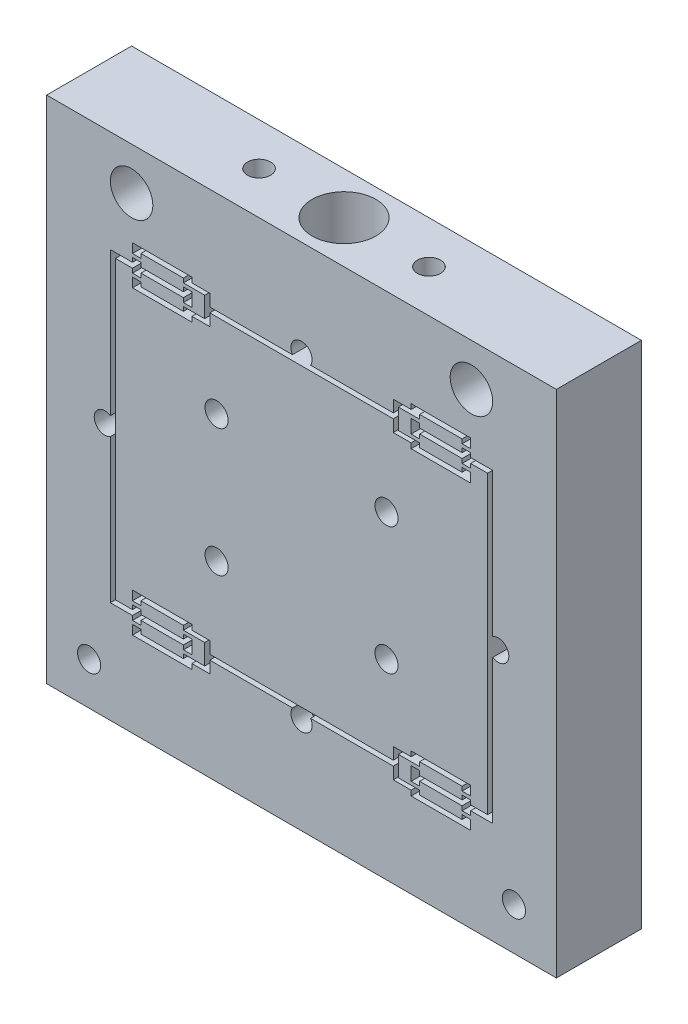
SolidWorks part; units mm, degrees
ref_plane "Front Plane" through (0, 0, 0) normal (0, 0, 1) x (1, 0, 0)
ref_plane "Top Plane" through (0, 0, 0) normal (0, 1, 0) x (1, 0, 0)
ref_plane "Right Plane" through (0, 0, 0) normal (1, 0, 0) x (0, 0, -1)
sketch "Sketch1" plane through (0, 0, 0) normal (0, 0, 1) x (1, 0, 0)
  line L1 (-38.1, 38.1) -> (38.1, 38.1)
  line L2 (-38.1, 38.1) -> (-38.1, -38.1)
  line L3 (-38.1, -38.1) -> (38.1, -38.1)
  line L4 (38.1, 38.1) -> (38.1, -38.1)
  dimension "D1" = 38.1
  dimension "D2" = 38.1
  dimension "D3" = 38.1
  dimension "D4" = 38.1
extrude "Boss-Extrude1" add sketch "Sketch1" along normal mid plane 12.7
sketch "Sketch2" plane through (0, 0, 6.35) normal (0, 0, 1) x (1, 0, 0)
  line L0 (16.383, 23.495) -> (17.653, 23.495)
  line L1 (28.575, 22.86) -> (28.575, -22.86)
  line L2 (0, 0) -> (38.1, 0) construction
  line L3 (25.273, -22.86) -> (28.575, -22.86)
  line L4 (25.273, -22.098) -> (27.813, -22.098)
  line L5 (27.813, -22.098) -> (27.813, 22.098)
  line L6 (17.653, 23.495) -> (17.653, 22.86)
  line L7 (16.383, 21.463) -> (16.383, 23.495)
  line L8 (38.1, -38.1) -> (38.1, 38.1) construction
  line L9 (17.653, 22.86) -> (24.003, 22.86)
  line L10 (24.003, 22.86) -> (24.003, 23.495)
  line L11 (24.003, 23.495) -> (25.273, 23.495)
  line L12 (25.273, 23.495) -> (25.273, 22.86)
  line L13 (25.273, 22.86) -> (28.575, 22.86)
  line L14 (16.383, 21.463) -> (17.653, 21.463)
  line L15 (17.653, 21.463) -> (17.653, 22.098)
  line L16 (17.653, 22.098) -> (24.003, 22.098)
  line L17 (24.003, 22.098) -> (24.003, 21.463)
  line L18 (24.003, 21.463) -> (25.273, 21.463)
  line L19 (25.273, 21.463) -> (25.273, 22.098)
  line L20 (25.273, 22.098) -> (27.813, 22.098)
  line L21 (17.653, -23.495) -> (17.653, -22.86)
  line L22 (17.653, -22.86) -> (24.003, -22.86)
  line L23 (24.003, -22.86) -> (24.003, -23.495)
  line L24 (24.003, -23.495) -> (25.273, -23.495)
  line L25 (25.273, -23.495) -> (25.273, -22.86)
  line L26 (25.273, -21.463) -> (25.273, -22.098)
  line L27 (24.003, -21.463) -> (25.273, -21.463)
  line L28 (24.003, -22.098) -> (24.003, -21.463)
  line L29 (17.653, -22.098) -> (24.003, -22.098)
  line L30 (17.653, -21.463) -> (17.653, -22.098)
  line L31 (16.383, -21.463) -> (17.653, -21.463)
  line L32 (16.383, -21.463) -> (16.383, -23.495)
  line L33 (16.383, -23.495) -> (17.653, -23.495)
  dimension "D1" = 0.762
  dimension "D2" = 1.27
  dimension "D3" = 9.525
  dimension "D4" = 1.27
  dimension "D5" = 2.54
  dimension "D6" = 0.762
  dimension "D7" = 22.86
  dimension "D8" = 0.635
  dimension "D9" = 0.635
  dimension "D10" = 6.35
extrude "Cut-Extrude1" cut sketch "Sketch2" against normal up to next (12.7 mm away)
mirror "Mirror1" about plane through (0, 0, 0) normal (1, 0, 0) of "Cut-Extrude1"
sketch "Sketch3" plane through (0, 0, 6.35) normal (0, 0, 1) x (1, 0, 0)
  line L0 (25.273, 20.955) -> (25.273, 19.558)
  line L1 (25.273, 25.4) -> (16.383, 25.4)
  line L2 (16.383, 25.4) -> (16.383, 24.638)
  line L3 (-13.716, 22.86) -> (13.716, 22.86)
  line L6 (14.478, 24.003) -> (17.653, 24.003)
  line L7 (17.653, 24.003) -> (17.653, 24.638)
  line L8 (0, 38.1) -> (0, 0) construction
  line L9 (38.1, 38.1) -> (-38.1, 38.1) construction
  line L10 (25.273, 22.86) -> (25.273, 23.495) construction
  line L11 (24.003, 22.098) -> (24.003, 21.463) construction
  line L12 (17.653, 21.463) -> (17.653, 22.098) construction
  line L13 (13.716, 22.098) -> (-13.716, 22.098)
  line L14 (16.383, 24.638) -> (13.716, 24.638)
  line L15 (13.716, 24.638) -> (13.716, 22.86)
  line L16 (25.273, 25.4) -> (25.273, 24.003)
  line L17 (17.653, 24.638) -> (24.003, 24.638)
  line L18 (14.478, 24.003) -> (14.478, 20.955)
  line L19 (14.478, 20.955) -> (17.653, 20.955)
  line L20 (24.003, 21.463) -> (25.273, 21.463) construction
  line L21 (25.273, 23.495) -> (24.003, 23.495) construction
  line L25 (16.383, 23.495) -> (16.383, 21.463) construction
  line L26 (24.003, 24.638) -> (24.003, 24.003)
  line L27 (24.003, 24.003) -> (25.273, 24.003)
  line L28 (17.653, 20.955) -> (17.653, 20.32)
  line L29 (17.653, 20.32) -> (24.003, 20.32)
  line L30 (24.003, 20.32) -> (24.003, 20.955)
  line L31 (24.003, 20.955) -> (25.273, 20.955)
  line L32 (-16.383, 19.558) -> (-25.273, 19.558)
  line L33 (-16.383, 20.32) -> (-16.383, 19.558)
  line L34 (-25.273, 20.955) -> (-25.273, 19.558)
  line L35 (-24.003, 20.955) -> (-25.273, 20.955)
  line L36 (-24.003, 20.32) -> (-24.003, 20.955)
  line L37 (-17.653, 20.32) -> (-24.003, 20.32)
  line L38 (-17.653, 20.955) -> (-17.653, 20.32)
  line L39 (-14.478, 20.955) -> (-17.653, 20.955)
  line L40 (-14.478, 24.003) -> (-14.478, 20.955)
  line L41 (-14.478, 24.003) -> (-17.653, 24.003)
  line L42 (-17.653, 24.003) -> (-17.653, 24.638)
  line L43 (-17.653, 24.638) -> (-24.003, 24.638)
  line L44 (-24.003, 24.638) -> (-24.003, 24.003)
  line L45 (-24.003, 24.003) -> (-25.273, 24.003)
  line L46 (-25.273, 25.4) -> (-25.273, 24.003)
  line L47 (-13.716, 20.32) -> (-16.383, 20.32)
  line L48 (-13.716, 22.098) -> (-13.716, 20.32)
  line L49 (17.653, 22.098) -> (24.003, 22.098) construction
  line L50 (24.003, 22.86) -> (17.653, 22.86) construction
  line L51 (13.716, 22.098) -> (13.716, 20.32)
  line L52 (13.716, 20.32) -> (16.383, 20.32)
  line L53 (16.383, 20.32) -> (16.383, 19.558)
  line L54 (16.383, 19.558) -> (25.273, 19.558)
  line L55 (-13.716, 24.638) -> (-13.716, 22.86)
  line L56 (-16.383, 24.638) -> (-13.716, 24.638)
  line L57 (-16.383, 25.4) -> (-16.383, 24.638)
  line L58 (-25.273, 25.4) -> (-16.383, 25.4)
  point P26 (0, 17.78)
  point P35 (0, 19.05)
  dimension "D1" = 0.762
  dimension "D2" = 0.762
  dimension "D3" = 0.508
  dimension "D4" = 0.508
  dimension "D5" = 0.635
  dimension "D6" = 0.635
  dimension "D7" = 1.905
  dimension "D8" = 0.762
extrude "Cut-Extrude2" cut sketch "Sketch3" against normal up to next (12.7 mm away)
mirror "Mirror2" about plane through (0, 0, 0) normal (0, 1, 0) of "Cut-Extrude2"
hole_wizard "1/4 (0.25) Diameter Hole1" positions "Sketch5" profile "Sketch4" hole size "1/4" standard "ANSI Inch" end condition up to next
sketch "Sketch5" plane through (0, 0, 6.35) normal (0, 0, 1) x (1, 0, 0)
  line L0 (38.1, 38.1) -> (-38.1, 38.1) construction
  point P0 (-25.4, 31.75)
  point P2 (25.4, 31.75)
  dimension "D1" = 25.4
  dimension "D2" = 25.4
  dimension "D3" = 6.35
sketch "Sketch4" plane through (-25.4, 31.75, 6.35) normal (1, 0, 0) x (0, -1, 0)
  line L0 (0, 0) -> (0, 12.7)
  line L1 (0, 12.7) -> (3.175, 12.7)
  line L2 (3.175, 12.7) -> (3.175, 0)
  line L5 (3.175, 0) -> (0, 0)
  line L11 (0, -6.35) -> (0, 107.95) construction
  dimension "Thru Hole Dia." = 6.35
  dimension "Thru Hole Depth" = 12.7
hole_wizard "#8-32 Tapped Hole1" positions "Sketch7" profile "Sketch6" tap size "#8-32" standard "ANSI Inch" end condition up to next
sketch "Sketch7" plane through (0, 0, 6.35) normal (0, 0, 1) x (1, 0, 0)
  line L0 (-38.1, 38.1) -> (-38.1, -38.1) construction
  line L1 (38.1, -38.1) -> (38.1, 38.1) construction
  line L2 (-38.1, -38.1) -> (38.1, -38.1) construction
  point P0 (-12.7, 9.525)
  point P2 (12.7, 9.525)
  point P4 (12.7, -9.525)
  point P6 (-12.7, -9.525)
  point P20 (-31.75, -31.75)
  point P22 (31.75, -31.75)
  dimension "D1" = 12.7
  dimension "D2" = 12.7
  dimension "D3" = 9.525
  dimension "D4" = 9.525
  dimension "D5" = 6.35
  dimension "D6" = 6.35
  dimension "D7" = 6.35
sketch "Sketch6" plane through (-12.7, 9.525, 6.35) normal (1, 0, 0) x (0, -1, 0)
  line L0 (0, 0) -> (0, 12.7)
  line L1 (0, 12.7) -> (1.7272, 12.7)
  line L2 (1.7272, 12.7) -> (1.7272, 0)
  line L5 (1.7272, 0) -> (0, 0)
  line L11 (0, -6.35) -> (0, 107.95) construction
  dimension "Thru Tap Drill Dia." = 3.4544
  dimension "Thru Tap Drill Depth" = 12.7
cosmetic thread "Hole Thread1" parameters "D2"=4.1656
cosmetic thread "Hole Thread2" parameters "D2"=4.1656
cosmetic thread "Hole Thread3" parameters "D2"=4.1656
cosmetic thread "Hole Thread4" parameters "D2"=4.1656
cosmetic thread "Hole Thread5" parameters "D2"=4.1656
cosmetic thread "Hole Thread6" parameters "D2"=4.1656
sketch "Sketch12" plane through (0, 38.1, 0) normal (0, 1, 0) x (1, 0, 0)
  circle A0 centre (0, 0) radius 3.81
extrude "Cut-Extrude7" cut sketch "Sketch12" against normal blind 20.828
hole_wizard "#8-32 Tapped Hole2" positions "Sketch15" profile "Sketch14" tap size "#8-32" standard "ANSI Inch"
sketch "Sketch15" plane through (0, 38.1, 0) normal (0, 1, 0) x (1, 0, 0)
  point P0 (-12.7, 0)
  point P2 (12.7, 0)
  dimension "D1" = 12.7
  dimension "D2" = 12.7
sketch "Sketch14" plane through (-12.7, 38.1, 0) normal (1, 0, 0) x (0, 0, 1)
  line L0 (0, 0) -> (0, 11.1978)
  line L1 (0, 11.1978) -> (1.7272, 10.16)
  line L2 (1.7272, 10.16) -> (1.7272, 0)
  line L5 (1.7272, 0) -> (0, 0)
  line L10 (0, 11.1978) -> (-1.7272, 10.16) construction
  line L11 (0, -6.35) -> (0, 107.95) construction
  dimension "Tap Drill Dia." = 3.4544
  dimension "Tap Drill Depth" = 10.16
  dimension "Drill Angle" = 118
cosmetic thread "Hole Thread7" parameters "D1"=8.382, "D2"=4.1656
cosmetic thread "Hole Thread8" parameters "D1"=8.382, "D2"=4.1656
mirror "Mirror4" about plane through (0, 0, 0) normal (0, 1, 0) of "#8-32 Tapped Hole2", "Cut-Extrude7"
sketch "Sketch16" plane through (0, 0, 6.35) normal (0, 0, 1) x (1, 0, 0)
  line L0 (27.813, 22.098) -> (27.813, -22.098) construction
  line L1 (-13.716, 22.098) -> (13.716, 22.098) construction
  line L2 (-13.716, -22.098) -> (13.716, -22.098) construction
  line L3 (-27.813, 22.098) -> (-27.813, -22.098) construction
  circle A0 centre (0, 23.6855) radius 1.5875
  circle A1 centre (29.4005, 0) radius 1.5875
  circle A2 centre (-29.4005, 0) radius 1.5875
  circle A3 centre (0, -23.6855) radius 1.5875
extrude "Cut-Extrude8" cut sketch "Sketch16" against normal through all
sketch "Sketch17" plane through (0, 38.1, 0) normal (0, 1, 0) x (1, 0, 0)
  circle A0 centre (0, 0) radius 4.7625
extrude "Cut-Extrude9" cut sketch "Sketch17" against normal blind 12.7
mirror "Mirror5" about plane through (0, 0, 0) normal (0, 1, 0) of "Cut-Extrude9"
